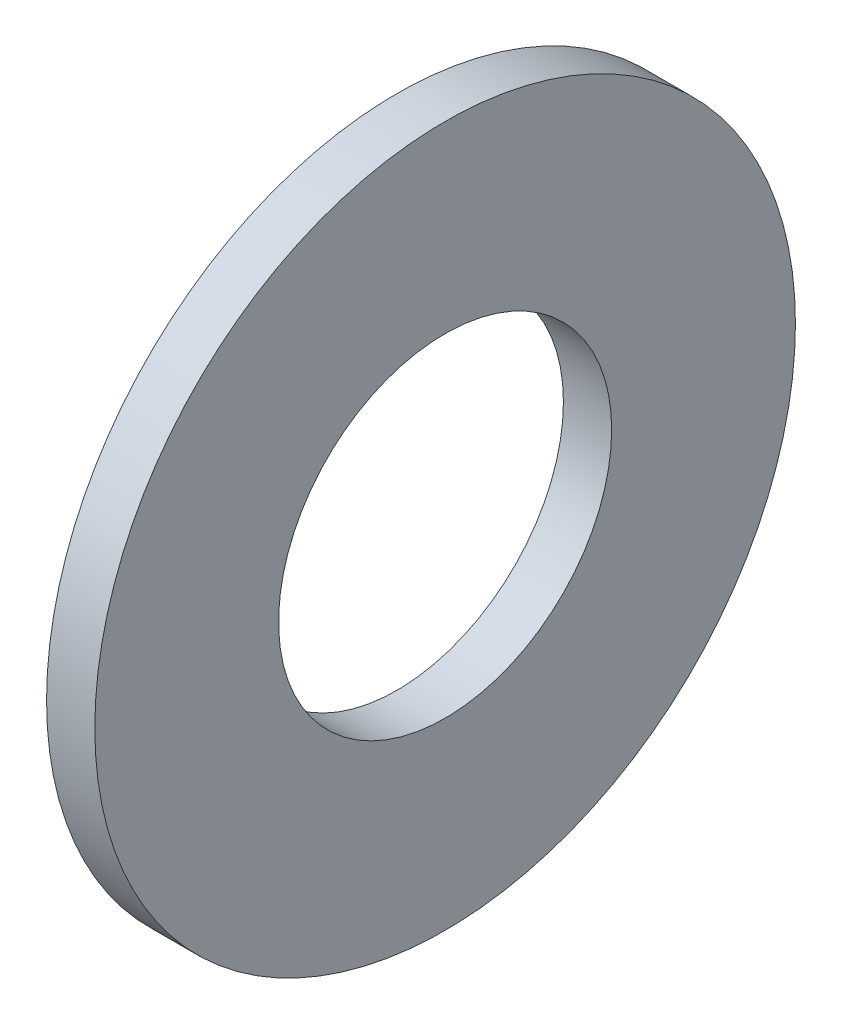
SolidWorks part; units mm, degrees
ref_plane "Front Plane" through (0, 0, 0) normal (0, 0, 1) x (1, 0, 0)
ref_plane "Top Plane" through (0, 0, 0) normal (0, 1, 0) x (1, 0, 0)
ref_plane "Right Plane" through (0, 0, 0) normal (1, 0, 0) x (0, 0, -1)
sketch "Sketch1" plane through (0, 0, 0) normal (1, 0, 0) x (0, 0, -1)
  circle A0 centre (0, 0) radius 30.5
  circle A1 centre (0, 0) radius 14.5
  dimension "D1" = 61
  dimension "D2" = 29
extrude "Boss-Extrude1" add sketch "Sketch1" against normal blind 4.2
